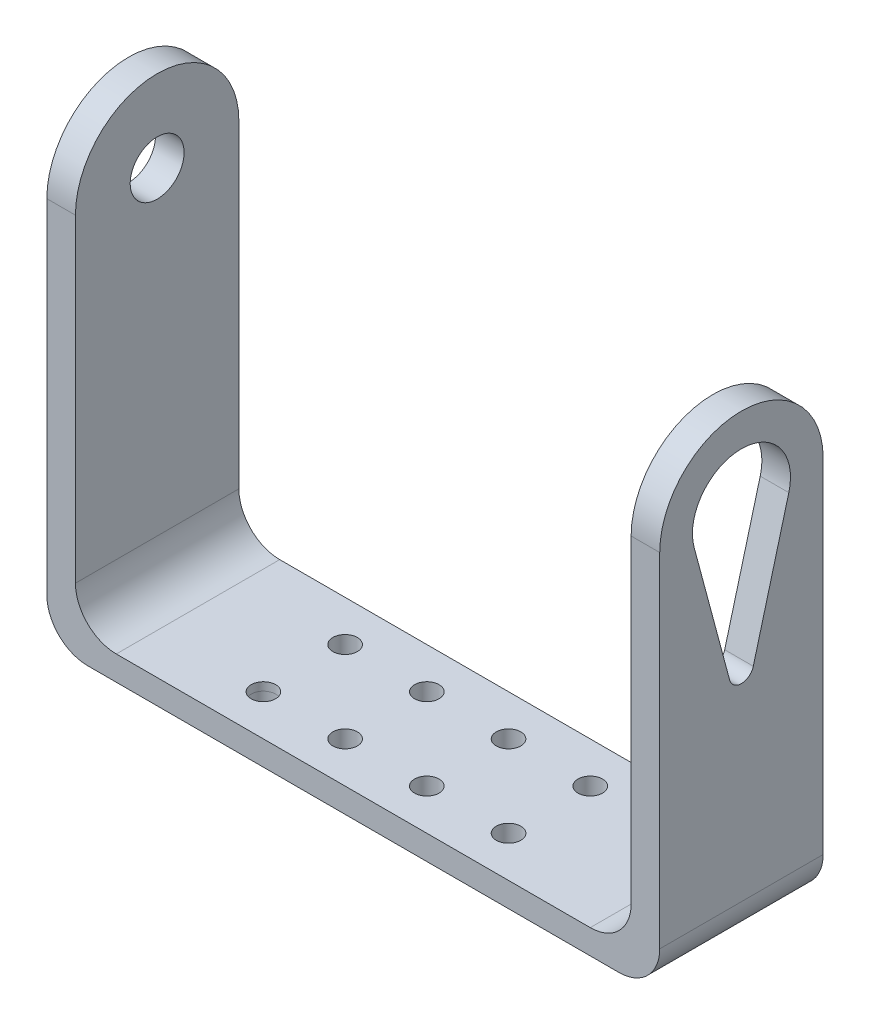
SolidWorks part; units mm, degrees
material "6061 합금"
ref_plane "정면" through (0, 0, 0) normal (0, 0, 1) x (1, 0, 0)
ref_plane "윗면" through (0, 0, 0) normal (0, 1, 0) x (1, 0, 0)
ref_plane "우측면" through (0, 0, 0) normal (1, 0, 0) x (0, 0, -1)
sketch "스케치2" plane through (0, 0, 0) normal (0, 1, 0) x (1, 0, 0)
  line L0 (0, 10) -> (0, -10) construction
  line L1 (35, -10) -> (-35, -10)
  line L3 (35, 10) -> (-35, 10)
  line L4 (-35, -10) -> (-35, 10)
  line L5 (35, -10) -> (-35, 10) construction
  line L6 (35, 10) -> (-35, -10) construction
  line L8 (35, 10) -> (38.5, 10)
  line L10 (35, -10) -> (38.5, -10)
  line L11 (38.5, 10) -> (38.5, -10)
  circle A0 centre (-15, 5) radius 1.5
  circle A1 centre (-5, 5) radius 1.5
  circle A2 centre (-15, -5) radius 1.5
  circle A3 centre (-5, -5) radius 1.5
  circle A4 centre (15, -5) radius 1.5
  circle A5 centre (5, -5) radius 1.5
  circle A6 centre (5, 5) radius 1.5
  circle A7 centre (15, 5) radius 1.5
  point P0 (0, 0)
  point P6 (-15, 5)
  point P7 (-5, 5)
  point P8 (-15, -5)
  point P9 (-5, -5)
  dimension "D9" = 5
  dimension "D1" = 70
  dimension "D2" = 20
  dimension "D3" = 3.5
  dimension "D4" = 5
  dimension "D5" = 10
  dimension "D6" = 5
  dimension "D7" = 10
  dimension "D8" = 10
extrude "보스-돌출1" add sketch "스케치2" along normal blind 2
ref_plane "평면1" through (0, 2, 0) normal (0, 1, 0) x (1, 0, 0)
sketch "스케치3" plane through (0, 2, 0) normal (0, 1, 0) x (1, 0, 0)
  line L0 (-35, -10) -> (38.5, -10) construction
  line L1 (-35, 10) -> (-33, 10)
  line L2 (-35, 10) -> (-35, -10)
  line L3 (-35, -10) -> (-33, -10)
  line L4 (-33, 10) -> (-33, -10)
  line L5 (-35, -10) -> (38.5, -10) construction
  line L6 (38.5, 10) -> (35, 10)
  line L7 (38.5, 10) -> (38.5, -10)
  line L8 (38.5, -10) -> (35, -10)
  line L9 (35, 10) -> (35, -10)
  dimension "D1" = 2
  dimension "D2" = 3.5
extrude "보스-돌출2" add sketch "스케치3" along normal blind 55
ref_plane "평면2" through (38.5, 0, 0) normal (1, 0, 0) x (0, 0, -1)
ref_plane "평면3" through (-35, 0, 0) normal (-1, 0, 0) x (0, 0, 1)
sketch "스케치9" plane through (38.5, 0, 0) normal (1, 0, 0) x (0, 0, -1)
  line L0 (-10, 57) -> (10, 57) construction
  line L1 (-10, 57) -> (-10, 0) construction
  line L4 (-10, 47) -> (-10, 57)
  line L5 (-10, 57) -> (10, 57)
  line L6 (10, 57) -> (10, 47)
  line L7 (-10, 47) -> (10, 47) construction
  arc A2 (10, 47) -> (-10, 47) centre (0, 47) ccw
  circle A3 centre (0, 47) radius 6
  point P10 (0, 47)
  point P17 (0, 54.07)
  point P18 (-7.07, 47)
  point P19 (0, 47)
  dimension "D6" = 12
  dimension "D4" = 7.07
  dimension "D5" = 7.07
extrude "컷-돌출1" cut sketch "스케치9" against normal blind 87 contours A2 L6 L5 | A2 L5 L4 | L7 A3 | A3 L7
sketch "스케치7" plane through (-35, 0, 0) normal (-1, 0, 0) x (0, 0, 1)
  circle A0 centre (0, 47) radius 6
  circle A1 centre (0, 47) radius 3.3
extrude "보스-돌출3" add sketch "스케치7" against normal blind 2
ref_plane "평면4" through (0, 0, 0) normal (0, -1, 0) x (-1, 0, 0)
ref_plane "평면5" through (-35, 0, 0) normal (-1, 0, 0) x (0, 0, 1)
sketch "스케치10" plane through (-35, 0, 0) normal (-1, 0, 0) x (0, 0, 1)
  line L0 (10, 0) -> (-10, 0)
  line L1 (-11, 0) -> (11, 0) construction
  line L2 (10, 47) -> (10, 0) construction
  line L3 (-10, 47) -> (-10, 0) construction
  line L4 (-10, 0) -> (-10, 47)
  line L6 (10, 47) -> (10, 0)
  arc A0 (-10, 47) -> (10, 47) centre (0, 47) cw
  circle A1 centre (0, 47) radius 3.3
extrude "보스-돌출4" add sketch "스케치10" along normal blind 1.5 contours A0 L4 L0 L6 A1
ref_plane "평면6" through (0, 2, 0) normal (0, 1, 0) x (1, 0, 0)
sketch "스케치11" plane through (0, 2, 0) normal (0, 1, 0) x (1, 0, 0)
  line L1 (-33, -10) -> (35, -10)
  line L2 (-33, -10) -> (-33, 10)
  line L3 (-33, 10) -> (35, 10)
  line L4 (35, -10) -> (35, 10)
  circle A0 centre (-15, 5) radius 1.5
  circle A1 centre (-5, 5) radius 1.5
  circle A2 centre (5, 5) radius 1.5
  circle A3 centre (15, 5) radius 1.5
  circle A4 centre (15, -5) radius 1.5
  circle A5 centre (5, -5) radius 1.5
  circle A6 centre (-5, -5) radius 1.5
  circle A7 centre (-15, -5) radius 1.4989
  dimension "D1" = 3
extrude "보스-돌출5" add sketch "스케치11" along normal blind 1
fillet "필렛6" radius 5 1 edges at (-33, 3, 0)
fillet "필렛7" radius 5 1 edges at (35, 3, 0)
fillet "필렛8" radius 5 2 edges at (38.5, 0, 0) (-36.5, 0, 0)
sketch "스케치12" plane through (38.5, 0, 0) normal (1, 0, 0) x (0, 0, -1)
  line L0 (1.4489, 29.2251) -> (5.7956, 45.4471)
  line L1 (-1.4489, 29.2251) -> (-5.7956, 45.4471)
  circle A0 centre (0, 47) radius 6 construction
  circle A1 centre (0, 47) radius 6
  arc A2 (-1.4489, 29.2251) -> (1.4489, 29.2251) centre (0, 29.6133) ccw
  dimension "D1" = 12
  dimension "D3" = 30
  dimension "D2" = 3
extrude "컷-돌출2" cut sketch "스케치12" against normal blind 3.5
